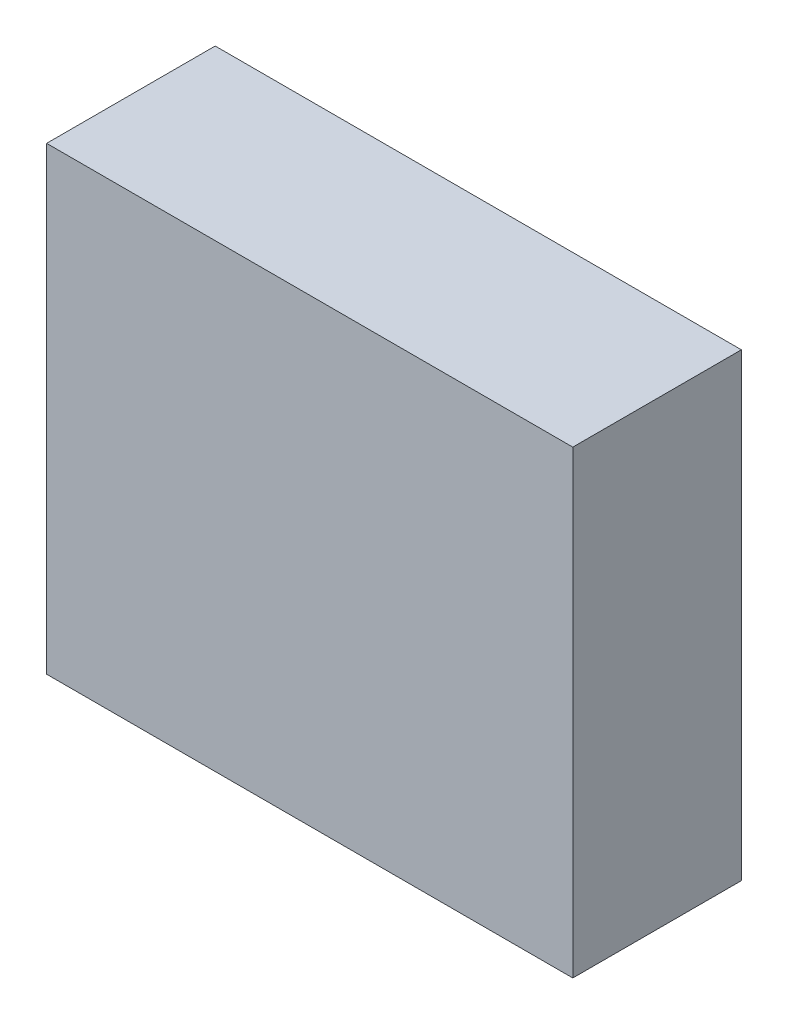
SolidWorks part; units mm, degrees
ref_plane "Спереди" through (0, 0, 0) normal (0, 0, 1) x (1, 0, 0)
ref_plane "Сверху" through (0, 0, 0) normal (0, 1, 0) x (1, 0, 0)
ref_plane "Справа" through (0, 0, 0) normal (1, 0, 0) x (0, 0, -1)
sketch "Эскиз1" plane through (0, 0, 0) normal (0, 0, 1) x (1, 0, 0)
  line L1 (-11.2498, -9.3479) -> (-0.9498, -9.3479)
  line L2 (-11.2498, -9.3479) -> (-11.2498, -18.3479)
  line L3 (-11.2498, -18.3479) -> (-0.9498, -18.3479)
  line L4 (-0.9498, -9.3479) -> (-0.9498, -18.3479)
extrude "Бобышка-Вытянуть1" add sketch "Эскиз1" along normal blind 3.3 contours L2 L3 L4 L1
